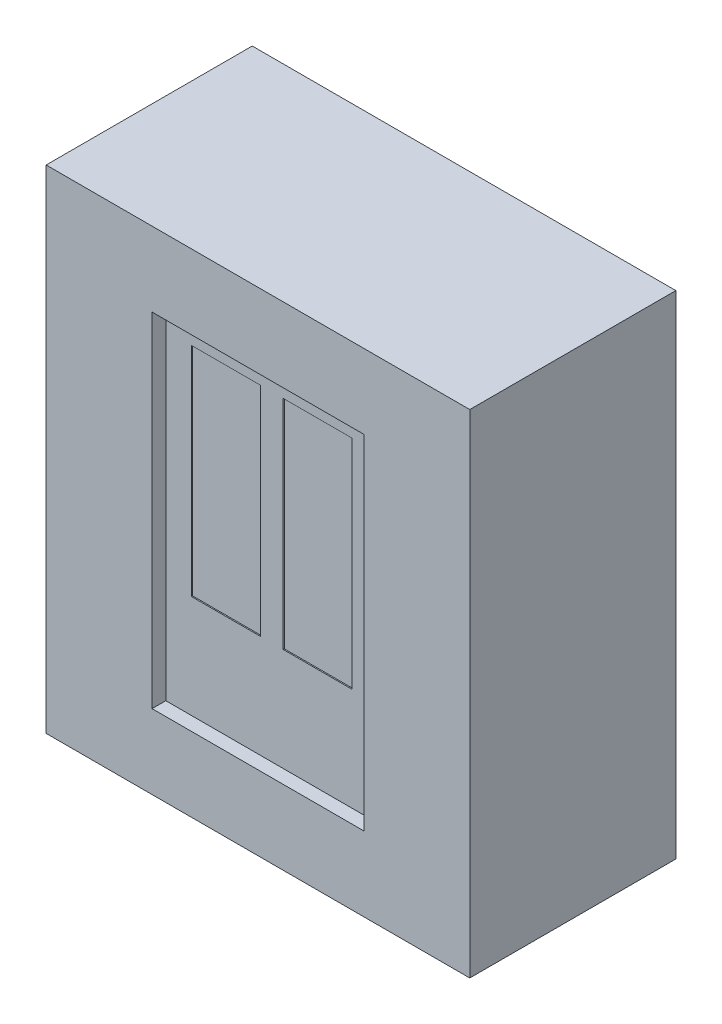
SolidWorks part; units mm, degrees
ref_plane "Alzado" through (0, 0, 0) normal (0, 0, 1) x (1, 0, 0)
ref_plane "Planta" through (0, 0, 0) normal (0, 1, 0) x (1, 0, 0)
ref_plane "Vista lateral" through (0, 0, 0) normal (1, 0, 0) x (0, 0, -1)
sketch "Croquis1" plane through (0, 0, 0) normal (0, 0, 1) x (1, 0, 0)
  line L1 (0, 0) -> (370, 0)
  line L2 (0, 0) -> (0, -430)
  line L3 (0, -430) -> (370, -430)
  line L4 (370, 0) -> (370, -430)
  dimension "D1" = 370
  dimension "D2" = 430
extrude "Saliente-Extruir1" add sketch "Croquis1" along normal blind 180
sketch "Croquis2" plane through (0, 0, 180) normal (0, 0, 1) x (1, 0, 0)
  line L0 (0, -215) -> (370, -215) construction
  line L1 (0, 0) -> (0, -430) construction
  line L2 (370, -430) -> (370, 0) construction
  line L4 (92.5, -65) -> (277.5, -65)
  line L5 (92.5, -65) -> (92.5, -365)
  line L6 (92.5, -365) -> (277.5, -365)
  line L7 (277.5, -65) -> (277.5, -365)
  line L8 (92.5, -65) -> (277.5, -365) construction
  line L9 (92.5, -365) -> (277.5, -65) construction
  point P6 (185, -215)
  dimension "D1" = 185
  dimension "D2" = 300
extrude "Cortar-Extruir1" cut sketch "Croquis2" against normal blind 12
sketch "Croquis3" plane through (0, 0, 168) normal (0, 0, 1) x (1, 0, 0)
  line L0 (185, -65) -> (185, -365) construction
  line L1 (277.5, -65) -> (92.5, -65) construction
  line L2 (92.5, -365) -> (277.5, -365) construction
  line L3 (277.5, -65) -> (92.5, -65) construction
  line L4 (175, -85) -> (115, -85)
  line L5 (175, -85) -> (175, -275)
  line L6 (175, -275) -> (115, -275)
  line L7 (115, -85) -> (115, -275)
  line L8 (255, -85) -> (255, -275)
  line L9 (195, -275) -> (255, -275)
  line L10 (195, -85) -> (195, -275)
  line L11 (195, -85) -> (255, -85)
  dimension "D1" = 10
  dimension "D2" = 20
  dimension "D3" = 60
  dimension "D4" = 190
extrude "Cortar-Extruir2" cut sketch "Croquis3" against normal blind 1
